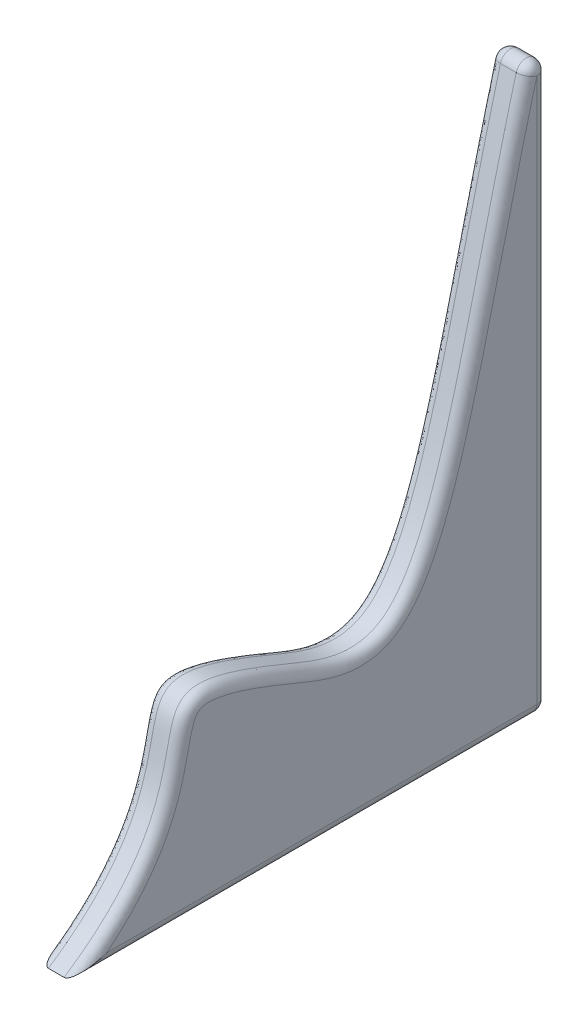
SolidWorks part; units mm, degrees
ref_plane "Front Plane" through (0, 0, 0) normal (0, 0, 1) x (1, 0, 0)
ref_plane "Top Plane" through (0, 0, 0) normal (0, 1, 0) x (1, 0, 0)
ref_plane "Right Plane" through (0, 0, 0) normal (1, 0, 0) x (0, 0, -1)
sketch "Sketch1" plane through (0, 0, 0) normal (1, 0, 0) x (0, 0, -1)
  line L2 (200, 300) -> (200, -300)
  line L3 (200, -300) -> (-250, -300)
  spline S0 degree 3 poles (-250, -300) (-77.0596, -184.8931) (-248.4592, -52.246) (99.9884, -208.3143) (136.2902, 88.1688) (200, 300) knots 0 0 0 0 0.685016 0.785016 1 1 1 1
  point P0 (0, 0)
  dimension "D1" = 450
extrude "Boss-Extrude1" add sketch "Sketch1" along normal blind 35 contours L3 S0 L2
fillet "Fillet1" radius 10 8 edges at (0, -300, 25) (35, -300, 25) (17.5, -300, -200) (35, 0, -200) (17.5, 300, -200) (0, 0, -200)
